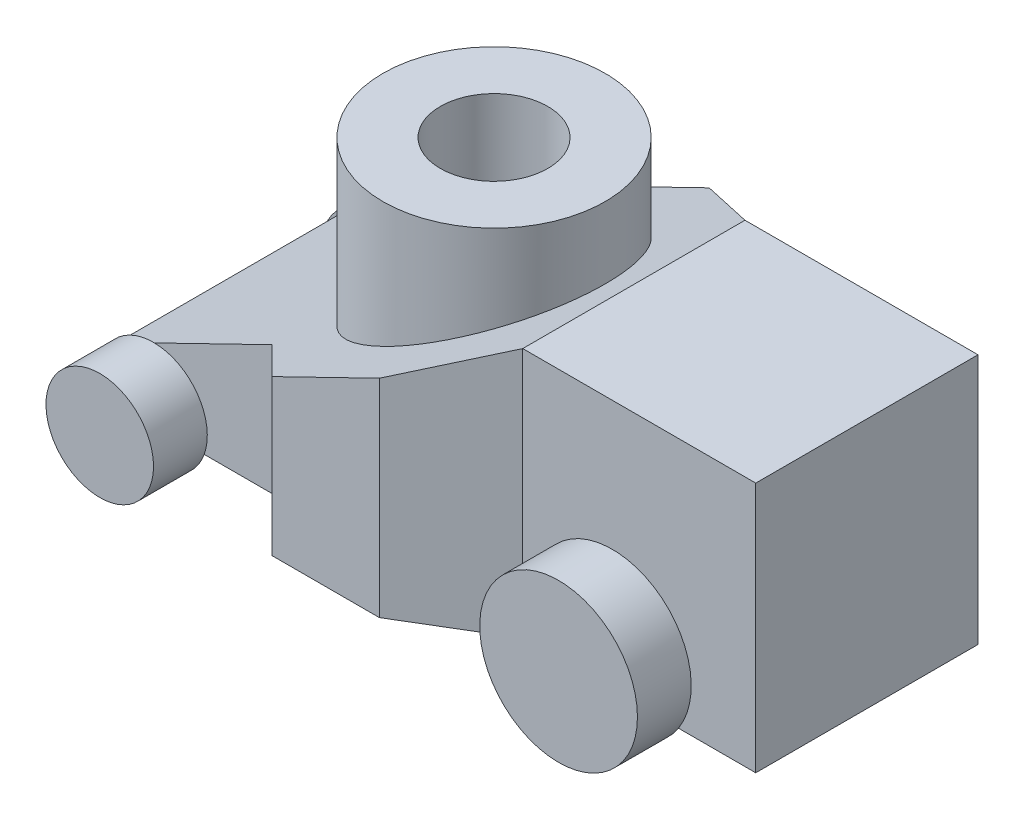
SolidWorks part; units mm, degrees
ref_plane "Front Plane" through (0, 0, 0) normal (0, 0, 1) x (1, 0, 0)
ref_plane "Top Plane" through (0, 0, 0) normal (0, 1, 0) x (1, 0, 0)
ref_plane "Right Plane" through (0, 0, 0) normal (1, 0, 0) x (0, 0, -1)
sketch "Sketch1" plane through (0, 0, 0) normal (0, 1, 0) x (1, 0, 0)
  line L0 (0, 0) -> (178, 0) construction
  line L1 (178, 31) -> (178, -31)
  line L2 (178, -31) -> (113, -31)
  line L3 (113, -31) -> (88, -46)
  line L4 (88, -46) -> (58, -46)
  line L5 (58, -46) -> (43, -31)
  line L6 (43, -31) -> (0, -31)
  line L7 (0, -31) -> (0, 31)
  line L8 (178, 31) -> (113, 31)
  line L9 (113, 31) -> (88, 46)
  line L10 (88, 46) -> (58, 46)
  line L11 (58, 46) -> (43, 31)
  line L12 (43, 31) -> (0, 31)
  dimension "D1" = 65
  dimension "D2" = 25
  dimension "D3" = 30
  dimension "D4" = 15
  dimension "D5" = 43
  dimension "D6" = 31
  dimension "D7" = 31
  dimension "D8" = 15
extrude "Extrude1" add sketch "Sketch1" along normal blind 70
sketch "Sketch2" plane through (0, 0, 31) normal (0, 0, 1) x (1, 0, 0)
  line L0 (113, 70) -> (0, 70)
  line L1 (0, 70) -> (0, 0) construction
  line L2 (0, 70) -> (0, 15)
  line L3 (0, 0) -> (43, 0) construction
  line L4 (113, 70) -> (0, 15)
  dimension "D1" = 15
extrude "Extrude2" cut sketch "Sketch2" against normal blind 90 and the other way blind 70
sketch "Sketch3" plane through (0, 0, 0) normal (0, 1, 0) x (1, 0, 0)
  line L0 (0, 0) -> (178, 0) construction
  line L1 (178, -31) -> (178, 31) construction
  line L2 (43, 31) -> (43, -31) construction
  circle A0 centre (74, 0) radius 31
  dimension "D1" = 62
extrude "Extrude3" add sketch "Sketch3" along normal blind 86
sketch "Sketch4" plane through (0, 86, 0) normal (0, 1, 0) x (1, 0, 0)
  circle A0 centre (74, 0) radius 15
  dimension "D1" = 30
extrude "Extrude4" cut sketch "Sketch4" against normal up to surface (34.9823 mm away)
sketch "Sketch5" plane through (0, 0, 31) normal (0, 0, 1) x (1, 0, 0)
  line L0 (12.2524, -10) -> (164.8024, -10) construction
  line L1 (43, 0) -> (58, 0) construction
  line L2 (0, 15) -> (0, 0) construction
  line L3 (178, 70) -> (178, 0) construction
  circle A0 centre (10, 5) radius 15
  circle A1 centre (138, 12) radius 22
  dimension "D2" = 30
  dimension "D3" = 44
  dimension "D4" = 10
  dimension "D5" = 40
  dimension "D1" = 10
extrude "Extrude5" add sketch "Sketch5" along normal blind 15
mirror "Mirror1" about plane through (0, 0, 0) normal (0, 0, 1) of "Extrude5"
